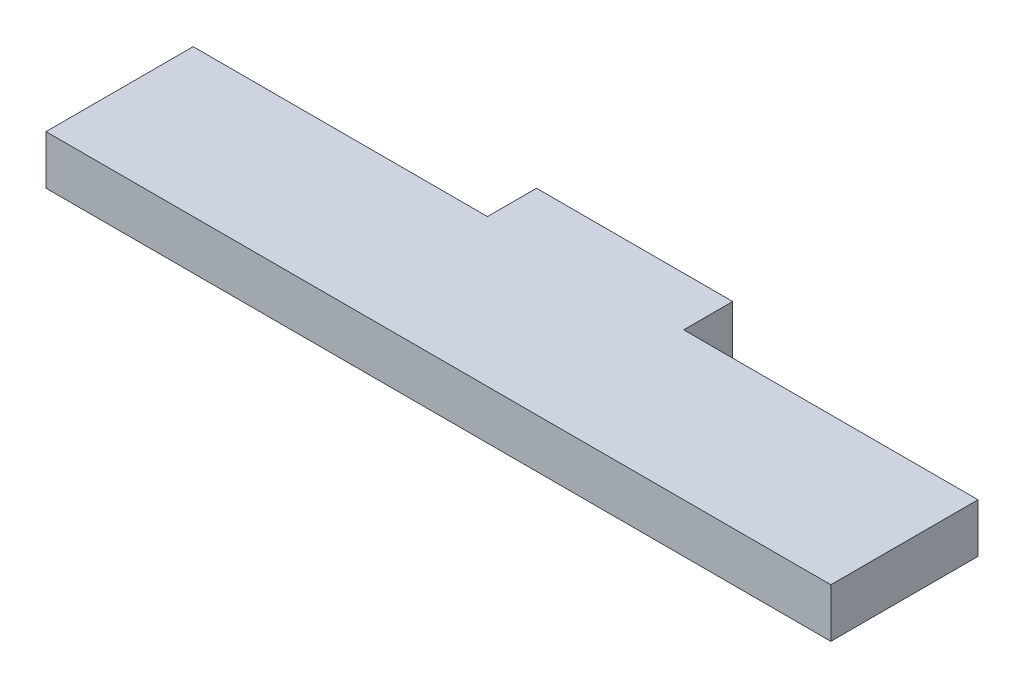
SolidWorks part; units mm, degrees
ref_plane "Front Plane" through (0, 0, 0) normal (0, 0, 1) x (1, 0, 0)
ref_plane "Top Plane" through (0, 0, 0) normal (0, 1, 0) x (1, 0, 0)
ref_plane "Right Plane" through (0, 0, 0) normal (1, 0, 0) x (0, 0, -1)
sketch "Sketch1" plane through (0, 0, 0) normal (0, 1, 0) x (1, 0, 0)
  line L1 (-21.1425, 19.05) -> (80.4575, 19.05)
  line L2 (-21.1425, 19.05) -> (-21.1425, -6.35)
  line L3 (-21.1425, -6.35) -> (80.4575, -6.35)
  line L4 (80.4575, 19.05) -> (80.4575, -6.35)
  dimension "D1" = 25.4
  dimension "D2" = 101.6
extrude "Boss-Extrude1" add sketch "Sketch1" along normal blind 6.35
sketch "Sketch2" plane through (0, 6.35, 0) normal (0, 1, 0) x (1, 0, 0)
  line L0 (80.4575, 19.05) -> (-21.1425, 19.05) construction
  line L1 (-21.1425, 19.05) -> (16.9575, 19.05)
  line L2 (-21.1425, 19.05) -> (-21.1425, 12.7)
  line L3 (-21.1425, 12.7) -> (16.9575, 12.7)
  line L4 (16.9575, 19.05) -> (16.9575, 12.7)
  line L5 (-21.1425, 19.05) -> (-21.1425, -6.35) construction
  line L6 (80.4575, -6.35) -> (80.4575, 19.05) construction
  line L7 (42.3575, 19.05) -> (80.4575, 19.05)
  line L8 (42.3575, 19.05) -> (42.3575, 12.7)
  line L9 (42.3575, 12.7) -> (80.4575, 12.7)
  line L10 (80.4575, 19.05) -> (80.4575, 12.7)
  point P12 (80.4575, 15.875)
  dimension "D1" = 38.1
  dimension "D2" = 6.35
  dimension "D3" = 6.35
  dimension "D4" = 38.1
extrude "Cut-Extrude1" cut sketch "Sketch2" against normal through all both and the other way through all
sketch "Sketch3" plane through (0, 6.35, 0) normal (0, 1, 0) x (1, 0, 0)
  line L16 (16.7575, 19.25) -> (16.7575, 12.9)
  line L17 (16.7575, 12.9) -> (-21.3425, 12.9)
  line L18 (-21.3425, 12.9) -> (-21.3425, -6.55)
  line L19 (-21.3425, -6.55) -> (80.6575, -6.55)
  line L20 (80.6575, -6.55) -> (80.6575, 12.9)
  line L21 (80.6575, 12.9) -> (42.5575, 12.9)
  line L22 (42.5575, 12.9) -> (42.5575, 19.25)
  line L23 (42.5575, 19.25) -> (16.7575, 19.25)
  line L24 (16.7575, 19.25) -> (16.7575, 12.9)
  line L25 (16.7575, 12.9) -> (-21.3425, 12.9)
  line L26 (-21.3425, 12.9) -> (-21.3425, -6.55)
  line L27 (-21.3425, -6.55) -> (80.6575, -6.55)
  line L28 (80.6575, -6.55) -> (80.6575, 12.9)
  line L29 (80.6575, 12.9) -> (42.5575, 12.9)
  line L30 (42.5575, 12.9) -> (42.5575, 19.25)
  line L31 (42.5575, 19.25) -> (16.7575, 19.25)
  dimension "D1" = 0.2
